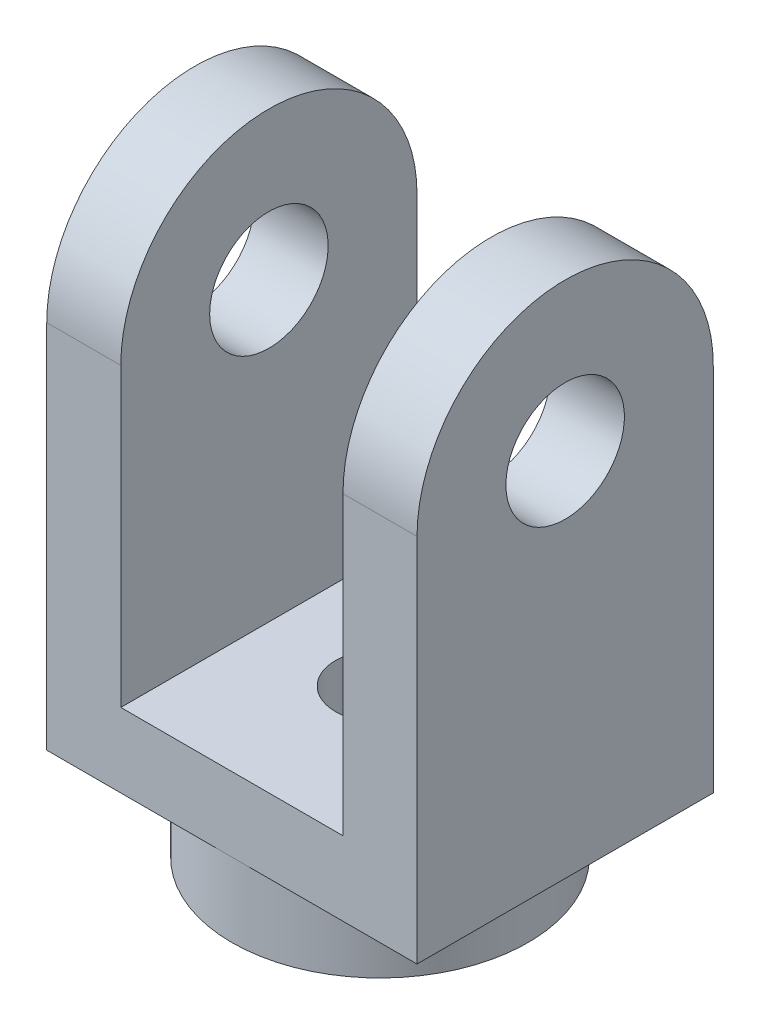
SolidWorks part; units mm, degrees
ref_plane "Front Plane" through (0, 0, 0) normal (0, 0, 1) x (1, 0, 0)
ref_plane "Top Plane" through (0, 0, 0) normal (0, 1, 0) x (1, 0, 0)
ref_plane "Right Plane" through (0, 0, 0) normal (1, 0, 0) x (0, 0, -1)
sketch "Sketch1" plane through (0, 0, 0) normal (0, 1, 0) x (1, 0, 0)
  circle A0 centre (0, 0) radius 37.5
  circle A1 centre (0, 0) radius 50
  dimension "D1" = 75
  dimension "D2" = 100
extrude "Boss-Extrude3" add sketch "Sketch1" along normal blind 25 contours A0 | A1
sketch "Sketch2" plane through (0, 0, 0) normal (0, -1, 0) x (1, 0, 0)
  circle A0 centre (0, 0) radius 37.5
  dimension "D1" = 75
extrude "Boss-Extrude4" add sketch "Sketch2" against normal blind 25
sketch "Sketch3" plane through (0, 25, 0) normal (0, 1, 0) x (1, 0, 0)
  line L0 (-62.5, 0) -> (62.5, 0) construction
  line L1 (-62.5, 50) -> (62.5, 50)
  line L2 (-62.5, 50) -> (-62.5, -50)
  line L3 (-62.5, -50) -> (62.5, -50)
  line L4 (62.5, 50) -> (62.5, -50)
  line L5 (0, 50) -> (0, -50) construction
  point P8 (0, 0)
  dimension "D1" = 125
  dimension "D2" = 100
extrude "Boss-Extrude5" add sketch "Sketch3" along normal blind 25 contours L2 L1 L4 L3
sketch "Sketch4" plane through (0, 50, 0) normal (0, 1, 0) x (1, 0, 0)
  line L0 (-62.5, -50) -> (62.5, -50) construction
  line L1 (-62.5, 50) -> (-37.5, 50)
  line L2 (-62.5, 50) -> (-62.5, -50)
  line L3 (-62.5, -50) -> (-37.5, -50)
  line L4 (-37.5, 50) -> (-37.5, -50)
  dimension "D1" = 25
extrude "Boss-Extrude6" add sketch "Sketch4" along normal blind 100
sketch "Sketch5" plane through (0, 50, 0) normal (0, 1, 0) x (1, 0, 0)
  line L0 (-37.5, -50) -> (62.5, -50) construction
  line L1 (62.5, 50) -> (37.5, 50)
  line L2 (62.5, 50) -> (62.5, -50)
  line L3 (62.5, -50) -> (37.5, -50)
  line L4 (37.5, 50) -> (37.5, -50)
  dimension "D1" = 25
extrude "Boss-Extrude7" add sketch "Sketch5" along normal blind 100
sketch "Sketch7" plane through (0, 50, 0) normal (0, 1, 0) x (1, 0, 0)
  circle A0 centre (0, 0) radius 15
  dimension "D1" = 30
extrude "Cut-Extrude1" cut sketch "Sketch7" against normal through all both and the other way through all
sketch "Sketch11" plane through (62.5, 0, 0) normal (1, 0, 0) x (0, 0, -1)
  line L4 (-50, 25) -> (50, 25)
  line L5 (50, 25) -> (50, 150)
  line L6 (50, 150) -> (-50, 150)
  line L7 (-50, 150) -> (-50, 25)
  line L8 (-50, 25) -> (50, 25)
  line L9 (50, 25) -> (50, 150)
  line L11 (-50, 150) -> (-50, 25)
  arc A0 (-50, 150) -> (50, 150) centre (0, 150) cw
  dimension "D1" = 0
extrude "Boss-Extrude12" add sketch "Sketch11" against normal blind 25
sketch "Sketch13" plane through (-62.5, 0, 0) normal (-1, 0, 0) x (0, 0, 1)
  line L4 (-50, 25) -> (50, 25)
  line L5 (50, 25) -> (50, 150)
  line L6 (50, 150) -> (-50, 150)
  line L7 (-50, 150) -> (-50, 25)
  line L10 (50, 150) -> (-50, 150)
  arc A0 (-50, 150) -> (50, 150) centre (0, 150) cw
  dimension "D1" = 0
extrude "Boss-Extrude13" add sketch "Sketch13" against normal blind 25
sketch "Sketch14" plane through (-62.5, 0, 0) normal (-1, 0, 0) x (0, 0, 1)
  line L0 (-50, 150) -> (50, 150) construction
  line L1 (0, 200) -> (0.0001, 200) construction
  line L2 (0, 200) -> (0, 150) construction
  arc A0 (50, 150) -> (-50, 150) centre (0, 150) ccw construction
  circle A1 centre (0, 150) radius 20
  dimension "D1" = 40
extrude "Cut-Extrude2" cut sketch "Sketch14" against normal through all both and the other way through all
